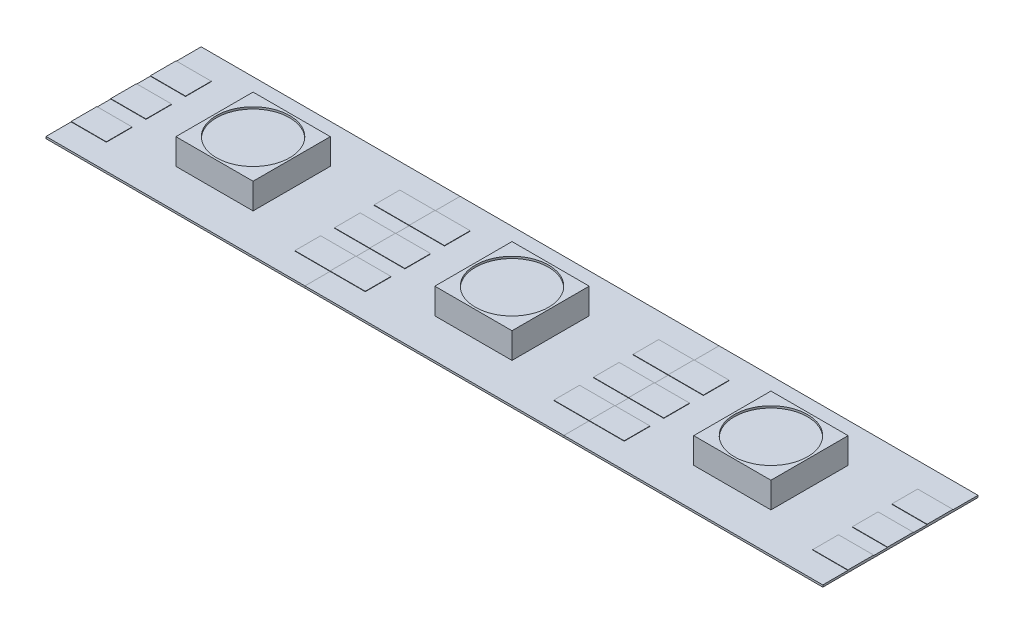
SolidWorks part; units mm, degrees
ref_plane "Front Plane" through (0, 0, 0) normal (0, 0, 1) x (1, 0, 0)
ref_plane "Top Plane" through (0, 0, 0) normal (0, 1, 0) x (1, 0, 0)
ref_plane "Right Plane" through (0, 0, 0) normal (1, 0, 0) x (0, 0, -1)
sketch "Sketch1" plane through (0, 0, 0) normal (0, 1, 0) x (1, 0, 0)
  line L0 (-8.3058, 4.9784) -> (8.3058, -4.9784) construction
  line L1 (-8.3058, 4.9784) -> (8.3058, 4.9784)
  line L2 (-8.3058, 4.9784) -> (-8.3058, -4.9784)
  line L3 (-8.3058, -4.9784) -> (8.3058, -4.9784)
  line L4 (8.3058, 4.9784) -> (8.3058, -4.9784)
  dimension "D1" = 9.9568
  dimension "D2" = 16.6116
extrude "Boss-Extrude1" add sketch "Sketch1" along normal blind 0.127
sketch "Sketch3" plane through (0, 0.127, 0) normal (0, 1, 0) x (1, 0, 0)
  line L0 (-8.3058, 4.9784) -> (8.3058, -4.9784) construction
  line L1 (-2.4765, 2.4765) -> (2.4765, -2.4765) construction
  line L2 (-2.4765, 2.4765) -> (2.4765, 2.4765)
  line L3 (-2.4765, 2.4765) -> (-2.4765, -2.4765)
  line L4 (-2.4765, -2.4765) -> (2.4765, -2.4765)
  line L5 (2.4765, 2.4765) -> (2.4765, -2.4765)
  dimension "D1" = 4.953
extrude "Boss-Extrude3" add sketch "Sketch3" along normal blind 1.651
sketch "Sketch4" plane through (0, 0.127, 0) normal (0, 1, 0) x (1, 0, 0)
  line L0 (-8.3058, 0) -> (8.3058, 0) construction
  line L1 (-8.3058, 4.9784) -> (-8.3058, -4.9784) construction
  line L2 (8.3058, -4.9784) -> (8.3058, 4.9784) construction
  line L3 (-6.047, 0) -> (-8.3058, 0) construction
  line L4 (-8.3058, 0.8255) -> (-6.047, 0.8255)
  line L5 (-8.3058, 0.8255) -> (-8.3058, -0.8255)
  line L6 (-8.3058, -0.8255) -> (-6.047, -0.8255)
  line L7 (-6.047, 0.8255) -> (-6.047, -0.8255)
  line L8 (-8.3058, 3.3655) -> (-6.047, 3.3655)
  line L9 (-6.047, 3.3655) -> (-6.047, 1.7145)
  line L10 (-8.3058, 1.7145) -> (-6.047, 1.7145)
  line L11 (-8.3058, 3.3655) -> (-8.3058, 1.7145)
  line L12 (-6.047, -3.3655) -> (-6.047, -1.7145)
  line L13 (-8.3058, -1.7145) -> (-6.047, -1.7145)
  line L14 (-8.3058, -3.3655) -> (-8.3058, -1.7145)
  line L15 (-8.3058, -3.3655) -> (-6.047, -3.3655)
  line L16 (0, 0) -> (0, -4.9784) construction
  line L17 (-8.3058, -4.9784) -> (8.3058, -4.9784) construction
  line L18 (8.3058, -3.3655) -> (8.3058, -1.7145)
  line L19 (8.3058, -3.3655) -> (6.047, -3.3655)
  line L20 (6.047, -3.3655) -> (6.047, -1.7145)
  line L21 (8.3058, -1.7145) -> (6.047, -1.7145)
  line L22 (8.3058, 0.8255) -> (8.3058, -0.8255)
  line L23 (8.3058, -0.8255) -> (6.047, -0.8255)
  line L24 (6.047, 0.8255) -> (6.047, -0.8255)
  line L25 (8.3058, 0.8255) -> (6.047, 0.8255)
  line L26 (8.3058, 1.7145) -> (6.047, 1.7145)
  line L27 (6.047, 3.3655) -> (6.047, 1.7145)
  line L28 (8.3058, 3.3655) -> (8.3058, 1.7145)
  line L29 (8.3058, 3.3655) -> (6.047, 3.3655)
  dimension "D1" = 1.651
  dimension "D2" = 2
extrude "Boss-Extrude4" add sketch "Sketch4" along normal blind 0.0254
sketch "Sketch5" plane through (0, 1.778, 0) normal (0, 1, 0) x (1, 0, 0)
  circle A0 centre (0, 0) radius 2.3483
extrude "Cut-Extrude1" cut sketch "Sketch5" against normal blind 0.127
pattern_linear "LPattern1" count 3 spacing 16.6116 along (1, 0, 0) of "Boss-Extrude3", "Boss-Extrude4", "Cut-Extrude1", "Boss-Extrude1"
